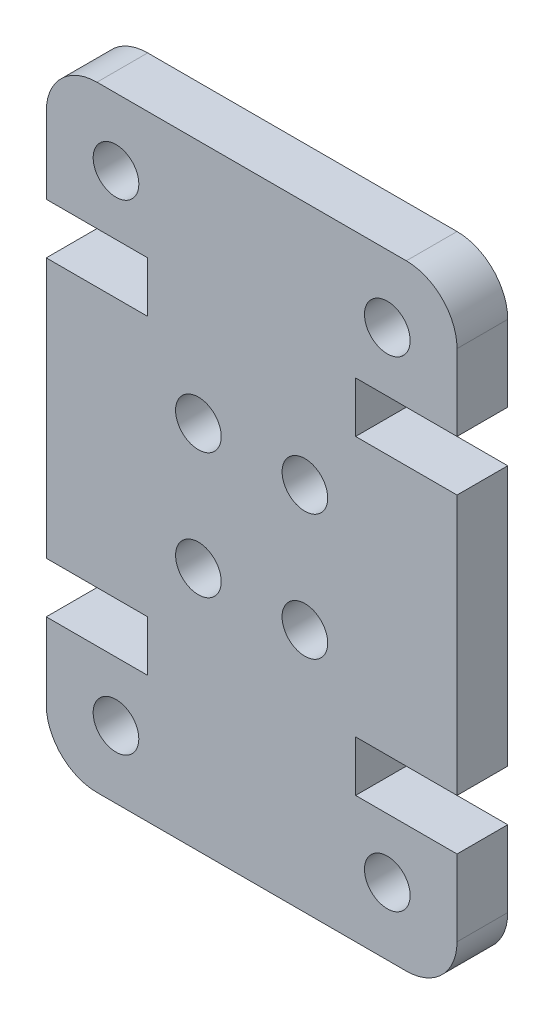
SolidWorks part; units mm, degrees
ref_plane "Front Plane" through (0, 0, 0) normal (0, 0, 1) x (1, 0, 0)
ref_plane "Top Plane" through (0, 0, 0) normal (0, 1, 0) x (1, 0, 0)
ref_plane "Right Plane" through (0, 0, 0) normal (1, 0, 0) x (0, 0, -1)
sketch "Sketch1" plane through (0, 0, 0) normal (0, 0, 1) x (1, 0, 0)
  line L0 (8.1, 24.26) -> (8.1, 0) construction
  line L1 (0, 12.13) -> (16.2, 12.13) construction
  line L2 (16.2, 17.26) -> (16.2, 7)
  line L3 (16.2, 2) -> (16.2, 5)
  line L4 (12.2, 5) -> (16.2, 5)
  line L5 (16.2, 7) -> (12.2, 7)
  line L6 (12.2, 7) -> (12.2, 5)
  line L7 (0, 22.26) -> (0, 19.26)
  line L8 (4, 19.26) -> (0, 19.26)
  line L9 (0, 17.26) -> (4, 17.26)
  line L10 (4, 17.26) -> (4, 19.26)
  line L11 (2, 24.26) -> (14.2, 24.26)
  line L12 (12.2, 17.26) -> (12.2, 19.26)
  line L13 (16.2, 17.26) -> (12.2, 17.26)
  line L14 (12.2, 19.26) -> (16.2, 19.26)
  line L15 (16.2, 22.26) -> (16.2, 19.26)
  line L21 (2, 0) -> (14.2, 0)
  line L25 (4, 7) -> (4, 5)
  line L28 (0, 7) -> (4, 7)
  line L30 (4, 5) -> (0, 5)
  line L34 (0, 2) -> (0, 5)
  line L38 (0, 17.26) -> (0, 7)
  circle A0 centre (13.45, 2.6536) radius 0.9
  circle A1 centre (10.2, 9.6536) radius 0.9
  arc A2 (16.2, 2) -> (14.2, 0) centre (14.2, 2) cw
  circle A3 centre (2.75, 21.6064) radius 0.9
  circle A4 centre (6, 14.6064) radius 0.9
  arc A5 (0, 22.26) -> (2, 24.26) centre (2, 22.26) cw
  arc A6 (16.2, 22.26) -> (14.2, 24.26) centre (14.2, 22.26) ccw
  circle A7 centre (10.2, 14.6064) radius 0.9
  circle A8 centre (13.45, 21.6064) radius 0.9
  arc A17 (0, 2) -> (2, 0) centre (2, 2) ccw
  circle A19 centre (6, 9.6536) radius 0.9
  circle A21 centre (2.75, 2.6536) radius 0.9
  point P16 (8.1, 12.13)
  dimension "D1" = 1.8
  dimension "D2" = 2
  dimension "D3" = 2.75
  dimension "D4" = 6
  dimension "D5" = 8.1
  dimension "D6" = 2.6536
  dimension "D7" = 5
  dimension "D9" = 9.6536
  dimension "D10" = 12.13
extrude "Boss-Extrude1" add sketch "Sketch1" along normal blind 2
equation "\"D5@Sketch1\"= \"fingerWidth@parametersSketch@prostheticParameters.SLDPRT\" / 2'PIP width"
equation "\"D10@Sketch1\"= ( \"HL@parametersSketch@prostheticParameters.SLDPRT\" * 0.196 - 4 - 8 ) / 2 'PIP length - Sil. Sht DIP - Sil. Sht PIP"
equation "\"D1@Sketch1\"= 1.5 + \"tol1@parametersSketch@prostheticParameters.SLDPRT\""
